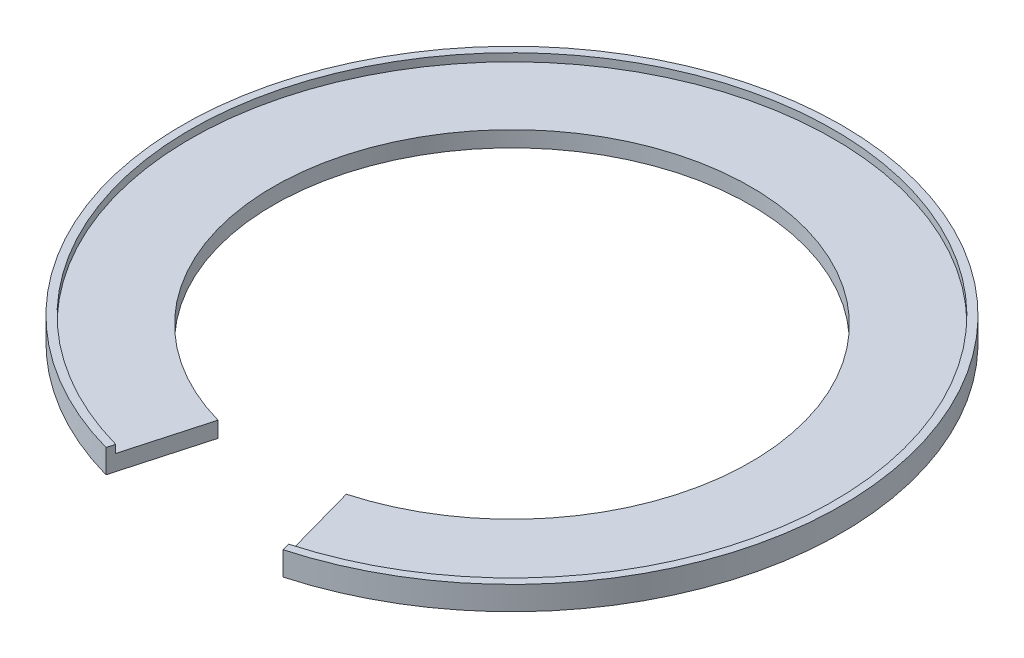
SolidWorks part; units mm, degrees
ref_plane "Plano frontal" through (0, 0, 0) normal (0, 0, 1) x (1, 0, 0)
ref_plane "Plano superior" through (0, 0, 0) normal (0, 1, 0) x (1, 0, 0)
ref_plane "Plano direito" through (0, 0, 0) normal (1, 0, 0) x (0, 0, -1)
sketch "Esboço1" plane through (0, 0, 0) normal (0, 1, 0) x (1, 0, 0)
  circle A0 centre (0, 0) radius 30.2284
  circle A1 centre (0, 0) radius 41.75
  dimension "D1" = 83.5
extrude "Ressalto-extrusão1" add sketch "Esboço1" along normal blind 2
sketch "Esboço3" plane through (0, 2, 0) normal (0, 1, 0) x (1, 0, 0)
  circle A0 centre (0, 0) radius 41.75
  circle A1 centre (0, 0) radius 40.75
  dimension "D1" = 1
  dimension "D2" = 81.5
extrude "Ressalto-extrusão2" add sketch "Esboço3" along normal blind 1
sketch "Esboço2" plane through (0, 2, 0) normal (0, 1, 0) x (1, 0, 0)
  line L0 (10.8832, -39.0103) -> (7.9273, -28.4149) construction
  line L1 (-7.9273, -28.4149) -> (-10.8832, -39.0103) construction
  line L2 (12.2931, -44.064) -> (7.9273, -28.4149)
  line L3 (-7.9273, -28.4149) -> (-12.2931, -44.064)
  arc A0 (-7.9273, -28.4149) -> (7.9273, -28.4149) centre (0, 0) ccw
  arc A1 (-12.2931, -44.064) -> (12.2931, -44.064) centre (0, 0) ccw
  point P1 (0, 0)
extrude "Corte-extrusão1" cut sketch "Esboço2" against normal through all and the other way through all
